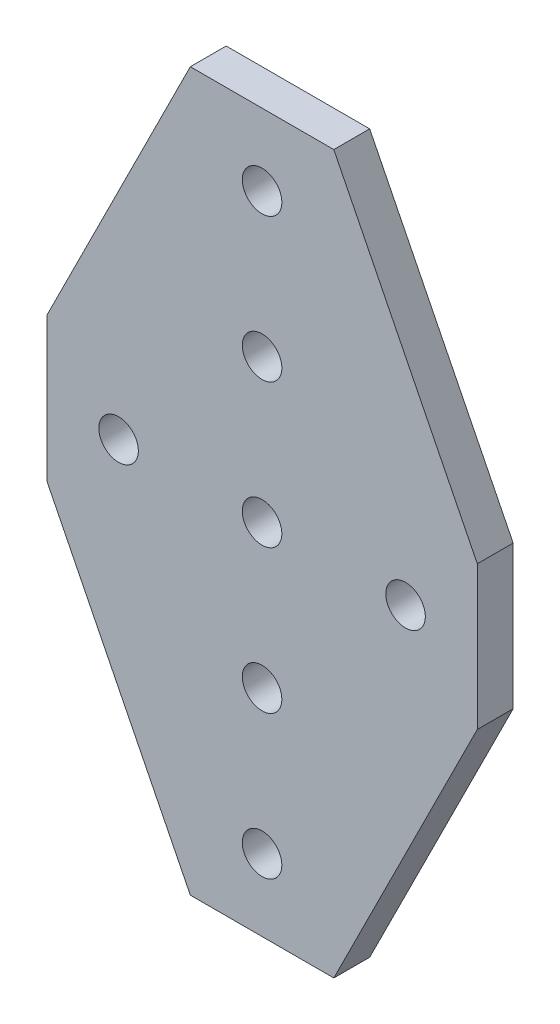
SolidWorks part; units mm, degrees
ref_plane "Front Plane" through (0, 0, 0) normal (0, 0, 1) x (1, 0, 0)
ref_plane "Top Plane" through (0, 0, 0) normal (0, 1, 0) x (1, 0, 0)
ref_plane "Right Plane" through (0, 0, 0) normal (1, 0, 0) x (0, 0, -1)
sketch "Sketch1" plane through (0, 0, 0) normal (0, 0, 1) x (1, 0, 0)
  line L0 (0, 0) -> (0, 50.8) construction
  line L1 (0, 50.8) -> (-25.4, 50.8) construction
  line L2 (-25.4, 50.8) -> (-25.4, 76.2)
  line L3 (-25.4, 76.2) -> (0, 76.2) construction
  line L4 (0, 76.2) -> (0, 127) construction
  line L5 (0, 127) -> (25.4, 127)
  line L6 (25.4, 127) -> (25.4, 76.2) construction
  line L7 (25.4, 76.2) -> (50.8, 76.2) construction
  line L8 (50.8, 76.2) -> (50.8, 50.8)
  line L9 (50.8, 50.8) -> (25.4, 50.8) construction
  line L10 (25.4, 50.8) -> (25.4, 0) construction
  line L11 (25.4, 0) -> (0, 0)
  line L12 (-25.4, 76.2) -> (0, 127)
  line L13 (25.4, 127) -> (50.8, 76.2)
  line L14 (50.8, 50.8) -> (25.4, 0)
  line L15 (0, 0) -> (-25.4, 50.8)
  dimension "D1" = 50.8
  dimension "D2" = 50.8
  dimension "D3" = 25.4
  dimension "D4" = 25.4
  dimension "D5" = 25.4
  dimension "D6" = 25.4
  dimension "D7" = 50.8
  dimension "D8" = 25.4
  dimension "D9" = 25.4
extrude "Boss-Extrude1" add sketch "Sketch1" along normal blind 6.35
sketch "Sketch2" plane through (0, 0, 6.35) normal (0, 0, 1) x (1, 0, 0)
  line L0 (12.7, 127) -> (12.7, 0) construction
  line L1 (25.4, 127) -> (0, 127) construction
  line L2 (0, 0) -> (25.4, 0) construction
  line L3 (50.8, 63.5) -> (-25.4, 63.5) construction
  line L4 (50.8, 50.8) -> (50.8, 76.2) construction
  line L5 (-25.4, 76.2) -> (-25.4, 50.8) construction
  line L6 (12.7, 63.5) -> (38.1, 63.5) construction
  line L7 (12.7, 63.5) -> (12.7, 38.1) construction
  circle A0 centre (12.7, 63.5) radius 3.5
  circle A1 centre (38.1, 63.5) radius 3.5
  circle A2 centre (-12.7, 63.5) radius 3.5
  circle A3 centre (12.7, 38.1) radius 3.5
  circle A4 centre (12.7, 12.7) radius 3.5
  circle A5 centre (12.7, 114.3) radius 3.5
  circle A6 centre (12.7, 88.9) radius 3.5
  dimension "D1" = 2
  dimension "D5" = 7
  dimension "D2" = 25.4
  dimension "D4" = 25.4
  dimension "D3" = 3
extrude "Cut-Extrude1" cut sketch "Sketch2" against normal through all
